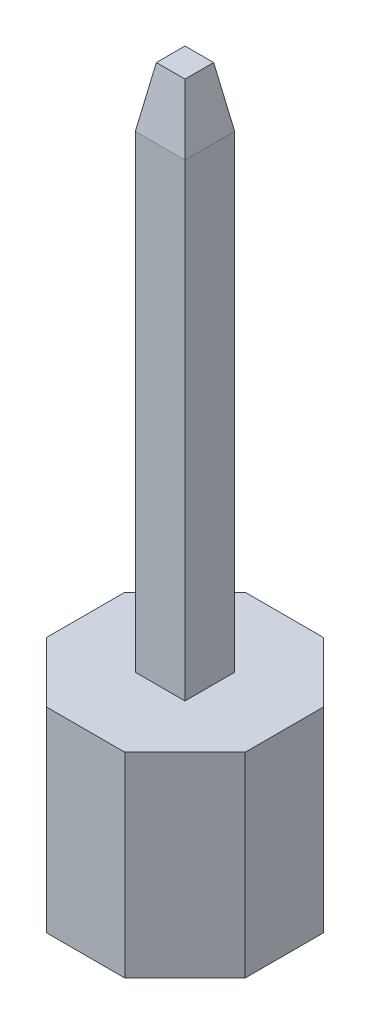
SolidWorks part; units mm, degrees
ref_plane "Front" through (0, 0, 0) normal (0, 0, 1) x (1, 0, 0)
ref_plane "Top" through (0, 0, 0) normal (0, 1, 0) x (1, 0, 0)
ref_plane "Right" through (0, 0, 0) normal (1, 0, 0) x (0, 0, -1)
sketch "Sketch1" plane through (0, 0, 0) normal (0, 1, 0) x (1, 0, 0)
  line L0 (-0.5, 1.27) -> (-1.27, 0.5)
  line L1 (-0.5, 1.27) -> (0.5, 1.27)
  line L2 (-1.27, 0.5) -> (-1.27, -0.5)
  line L3 (-1.27, 0) -> (1.27, 0) construction
  line L4 (0, 1.27) -> (0, -1.27) construction
  line L5 (-0.5, -1.27) -> (0.5, -1.27)
  line L6 (1.27, 0.5) -> (1.27, -0.5)
  line L7 (0.5, 1.27) -> (1.27, 0.5)
  line L8 (-0.5, -1.27) -> (-1.27, -0.5)
  line L9 (0.5, -1.27) -> (1.27, -0.5)
  circle A0 centre (0, 0) radius 0.3175
  dimension "D1" = 0.635
  dimension "D2" = 2.54
  dimension "D3" = 2.54
  dimension "D4" = 1
  dimension "D5" = 1
extrude "Boss-Extrude1" add sketch "Sketch1" along normal mid plane 2.5
sketch "Sketch2" plane through (0, 1.25, 0) normal (0, 1, 0) x (1, 0, 0)
  line L1 (-0.3175, 0.3175) -> (0.3175, 0.3175)
  line L2 (-0.3175, 0.3175) -> (-0.3175, -0.3175)
  line L3 (-0.3175, -0.3175) -> (0.3175, -0.3175)
  line L4 (0.3175, 0.3175) -> (0.3175, -0.3175)
  line L5 (-0.3175, 0.3175) -> (0.3175, -0.3175) construction
  line L6 (-0.3175, -0.3175) -> (0.3175, 0.3175) construction
  point P0 (0, 0)
  dimension "D1" = 0.635
  dimension "D2" = 0.635
extrude "Boss-Extrude2" add sketch "Sketch2" along normal blind 6.75 separate body
chamfer "Chamfer2" distance 0.762 angle 10 4 edges at (0, 8, 0.3175) (0.3175, 8, 0) (0, 8, -0.3175) (-0.3175, 8, 0)
